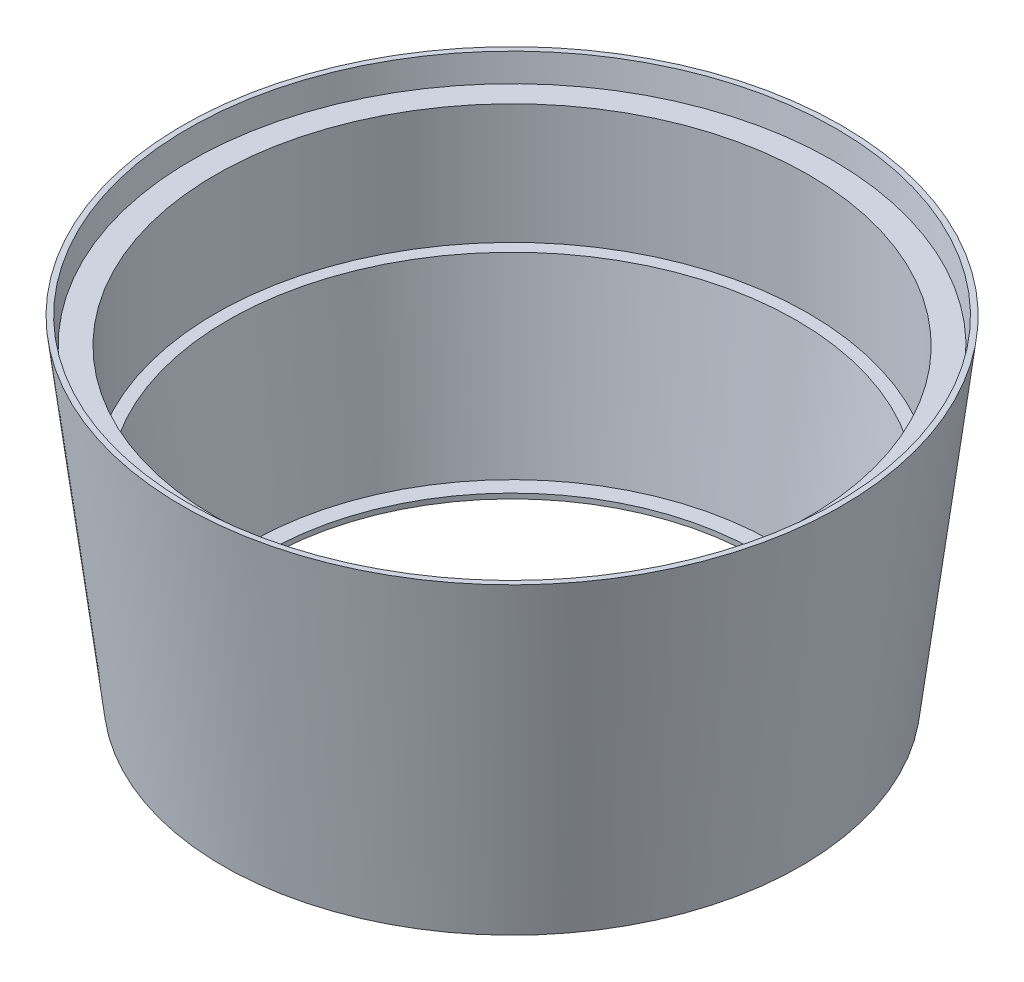
SolidWorks part; units mm, degrees
ref_plane "前视基准面" through (0, 0, 0) normal (0, 0, 1) x (1, 0, 0)
ref_plane "上视基准面" through (0, 0, 0) normal (0, 1, 0) x (1, 0, 0)
ref_plane "右视基准面" through (0, 0, 0) normal (1, 0, 0) x (0, 0, -1)
sketch "草图1" plane through (0, 0, 0) normal (0, 0, 1) x (1, 0, 0)
  line L0 (-69.8166, 0) -> (50, 0)
  line L1 (-69.8166, 0) -> (-69.8166, 14)
  line L2 (50, 0) -> (163.3086, 922.8244)
  line L3 (163.3086, 922.8244) -> (148.3086, 922.8244)
  line L4 (148.3086, 922.8244) -> (139.4475, 850.6565)
  line L5 (139.4475, 850.6565) -> (71.1231, 850.6565)
  line L6 (71.1231, 850.6565) -> (71.1231, 517.3111)
  line L7 (37.7019, 517.3111) -> (-24.0969, 14)
  line L8 (71.1231, 517.3111) -> (37.7019, 517.3111)
  line L9 (-69.8166, 14) -> (-24.0969, 14)
  line L10 (-69.8166, 0) -> (-752, 0) construction
  line L11 (-752, 0) -> (-752, 109.4948) construction
  point P3 (86.9662, 850.6565)
  point P14 (71.1231, 517.3111)
  point P15 (0, 0)
revolve "旋转1" add sketch "草图1" angle 360 about L11
